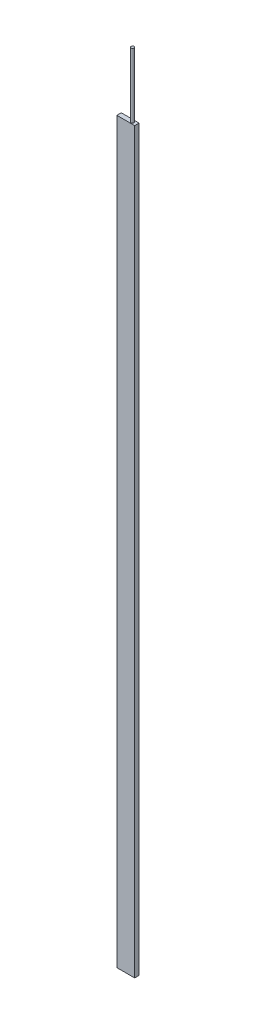
SolidWorks part; units mm, degrees
ref_plane "Front Plane" through (0, 0, 0) normal (0, 0, 1) x (1, 0, 0)
ref_plane "Top Plane" through (0, 0, 0) normal (0, 1, 0) x (1, 0, 0)
ref_plane "Right Plane" through (0, 0, 0) normal (1, 0, 0) x (0, 0, -1)
sketch "Sketch1" plane through (0, 0, 0) normal (0, 1, 0) x (1, 0, 0)
  line L1 (-69.0118, 17.0561) -> (69.0118, 17.0561)
  line L2 (-69.0118, 17.0561) -> (-69.0118, -17.0561)
  line L3 (-69.0118, -17.0561) -> (69.0118, -17.0561)
  line L4 (69.0118, 17.0561) -> (69.0118, -17.0561)
  line L5 (-69.0118, 17.0561) -> (69.0118, -17.0561) construction
  line L6 (-69.0118, -17.0561) -> (69.0118, 17.0561) construction
  point P0 (0, 0)
  dimension "D1" = 138.0236
  dimension "D2" = 34.1122
extrude "Boss-Extrude1" add sketch "Sketch1" along normal blind 5710
sketch "Sketch2" plane through (0, 5710, 0) normal (0, 1, 0) x (1, 0, 0)
  circle A3 centre (35.4584, 0) radius 11.43
  circle A4 centre (-35.4584, 0) radius 11.43
  dimension "D2" = 35.4584
  dimension "D1" = 35.4584
extrude "Boss-Extrude2" add sketch "Sketch2" along normal blind 500
